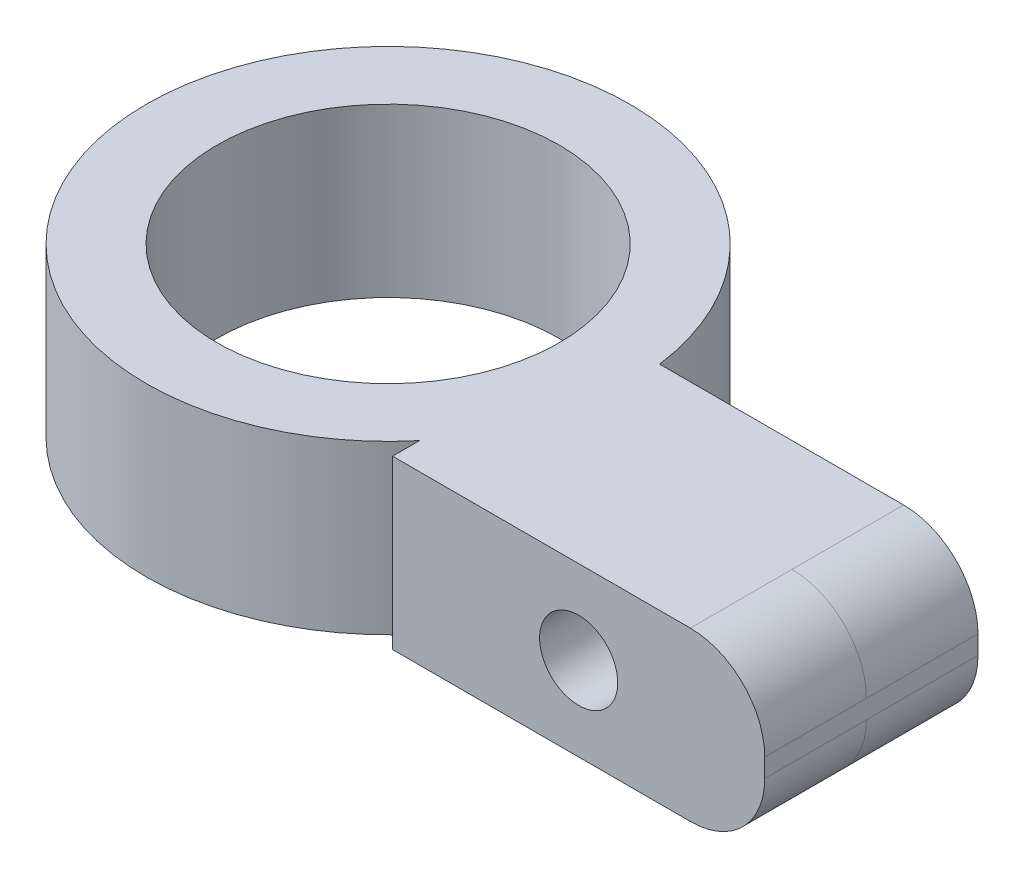
SolidWorks part; units mm, degrees
ref_plane "Front Plane" through (0, 0, 0) normal (0, 0, 1) x (1, 0, 0)
ref_plane "Top Plane" through (0, 0, 0) normal (0, 1, 0) x (1, 0, 0)
ref_plane "Right Plane" through (0, 0, 0) normal (1, 0, 0) x (0, 0, -1)
sketch "Sketch1" plane through (0, 0, 0) normal (0, 0, 1) x (1, 0, 0)
  line L1 (5, -2.25) -> (-5, -2.25)
  line L2 (5, -2.25) -> (5, 2.25)
  line L3 (5, 2.25) -> (-5, 2.25)
  line L4 (-5, -2.25) -> (-5, 2.25)
  line L5 (5, -2.25) -> (-5, 2.25) construction
  line L6 (5, 2.25) -> (-5, -2.25) construction
  point P0 (0, 0)
  dimension "D1" = 10
  dimension "D2" = 4.5
extrude "Boss-Extrude1" add sketch "Sketch1" along normal blind 3
fillet "Fillet1" radius 2 2 edges at (5, -2.25, 1.5) (5, 2.25, 1.5)
sketch "Sketch3" plane through (0, 0, 0) normal (0, 1, 0) x (1, 0, 0)
  line L0 (-5, -3) -> (-5, 0) construction
  line L1 (-5, 0) -> (3, 0) construction
  circle A0 centre (-10, -0.85) radius 6.5
  dimension "D2" = 13
  dimension "D1" = 5
  dimension "D3" = 0.85
extrude "Boss-Extrude2" add sketch "Sketch3" along normal mid plane 4.5 separate body
sketch "Sketch4" plane through (0, -2.25, 0) normal (0, -1, 0) x (1, 0, 0)
  line L0 (-5, 3) -> (-5, 0) construction
  circle A0 centre (-10, 0.85) radius 4.6
  dimension "D1" = 9.2
  dimension "D2" = 5
extrude "Cut-Extrude1" cut sketch "Sketch4" against normal through all
sketch "Sketch7" plane through (0, 0, 3) normal (0, 0, 1) x (1, 0, 0)
  circle A0 centre (0, 0) radius 1.05
  dimension "D1" = 2.1
sketch "Sketch8" plane through (0, 0, 3) normal (0, 0, 1) x (1, 0, 0)
  line L0 (-5, -2.25) -> (5, -2.25)
  line L1 (5, -2.25) -> (5, 2.25)
  line L2 (5, 2.25) -> (-5, 2.25)
  line L3 (3, 2.25) -> (-5, 2.25) construction
  line L4 (-5, 2.25) -> (-5, -2.25)
  line L5 (5, -0.25) -> (5, 0.25) construction
extrude "Boss-Extrude5" add sketch "Sketch8" along normal blind 2.73
sketch "Sketch9" plane through (0, 0, 5.73) normal (0, 0, 1) x (1, 0, 0)
  circle A0 centre (0, 0) radius 1.05
  dimension "D1" = 2.1
extrude "Cut-Extrude2" cut sketch "Sketch9" against normal blind 3
fillet "Fillet3" radius 2 2 edges at (5, 2.25, 4.365) (5, -2.25, 4.365)
